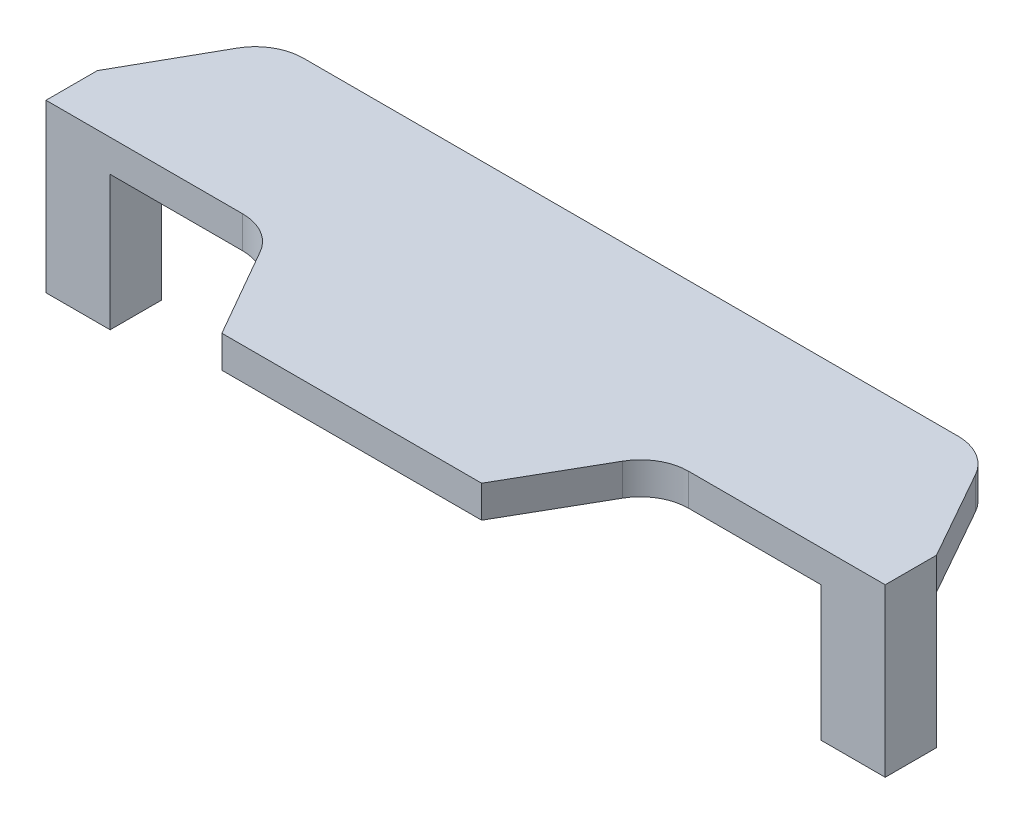
SolidWorks part; units mm, degrees
ref_plane "Front Plane" through (0, 0, 0) normal (0, 0, 1) x (1, 0, 0)
ref_plane "Top Plane" through (0, 0, 0) normal (0, 1, 0) x (1, 0, 0)
ref_plane "Right Plane" through (0, 0, 0) normal (1, 0, 0) x (0, 0, -1)
sketch "Sketch1" plane through (0, 0, 0) normal (0, 1, 0) x (1, 0, 0)
  line L0 (0, 0) -> (0, 12.7028) construction
  line L1 (-65.425, -4) -> (-55.425, -4)
  line L2 (-65.425, -4) -> (-65.425, 4)
  line L3 (-65.425, 4) -> (-55.425, 4)
  line L4 (-55.425, -4) -> (-55.425, 4)
  line L5 (-65.425, -4) -> (-55.425, 4) construction
  line L6 (-65.425, 4) -> (-55.425, -4) construction
  line L7 (65.425, 4) -> (55.425, -4) construction
  line L8 (65.425, -4) -> (55.425, 4) construction
  line L9 (55.425, -4) -> (55.425, 4)
  line L10 (65.425, 4) -> (55.425, 4)
  line L11 (65.425, -4) -> (65.425, 4)
  line L12 (65.425, -4) -> (55.425, -4)
  point P0 (-60.425, 0)
  point P12 (60.425, 0)
  dimension "D1" = 10
  dimension "D2" = 8
  dimension "D3" = 60.425
extrude "Boss-Extrude1" add sketch "Sketch1" along normal blind 21
sketch "Sketch2" plane through (0, 21, 0) normal (0, 1, 0) x (1, 0, 0)
  line L0 (-21.75, 21.75) -> (21.75, 21.75)
  line L1 (0, 21.75) -> (0, -21.75) construction
  line L2 (0, -21.75) -> (0, 21.75) construction
  line L3 (-20.25, -21.75) -> (20.25, -21.75)
  line L4 (-21.75, 21.75) -> (-20.25, -21.75) construction
  line L6 (-55.425, -4) -> (-55.425, 21.75) construction
  line L7 (-65.425, 4) -> (-65.425, -4)
  line L8 (-65.425, -4) -> (-34.7706, -4)
  line L9 (-28.2638, -7.7701) -> (-20.25, -21.75)
  line L10 (-65.425, 4) -> (-57.5764, 17.9313)
  line L11 (-51.042, 21.75) -> (-21.75, 21.75)
  line L12 (55.425, -4) -> (55.425, 21.75) construction
  line L13 (21.75, 21.75) -> (20.25, -21.75) construction
  line L14 (51.042, 21.75) -> (21.75, 21.75)
  line L15 (65.425, 4) -> (57.5764, 17.9313)
  line L16 (28.2638, -7.7701) -> (20.25, -21.75)
  line L17 (65.425, -4) -> (34.7706, -4)
  line L18 (65.425, 4) -> (65.425, -4)
  arc A0 (-28.2638, -7.7701) -> (-34.7706, -4) centre (-34.7706, -11.5) ccw
  arc A1 (-51.042, 21.75) -> (-57.5764, 17.9313) centre (-51.042, 14.25) ccw
  arc A2 (51.042, 21.75) -> (57.5764, 17.9313) centre (51.042, 14.25) cw
  arc A3 (28.2638, -7.7701) -> (34.7706, -4) centre (34.7706, -11.5) cw
  point P17 (-30.425, -4)
  point P31 (30.425, -4)
  dimension "D6" = 7.5
  dimension "D1" = 43.5
  dimension "D2" = 43.5
  dimension "D3" = 40.5
  dimension "D4" = 25.75
  dimension "D5" = 35
extrude "Boss-Extrude2" add sketch "Sketch2" along normal blind 5
